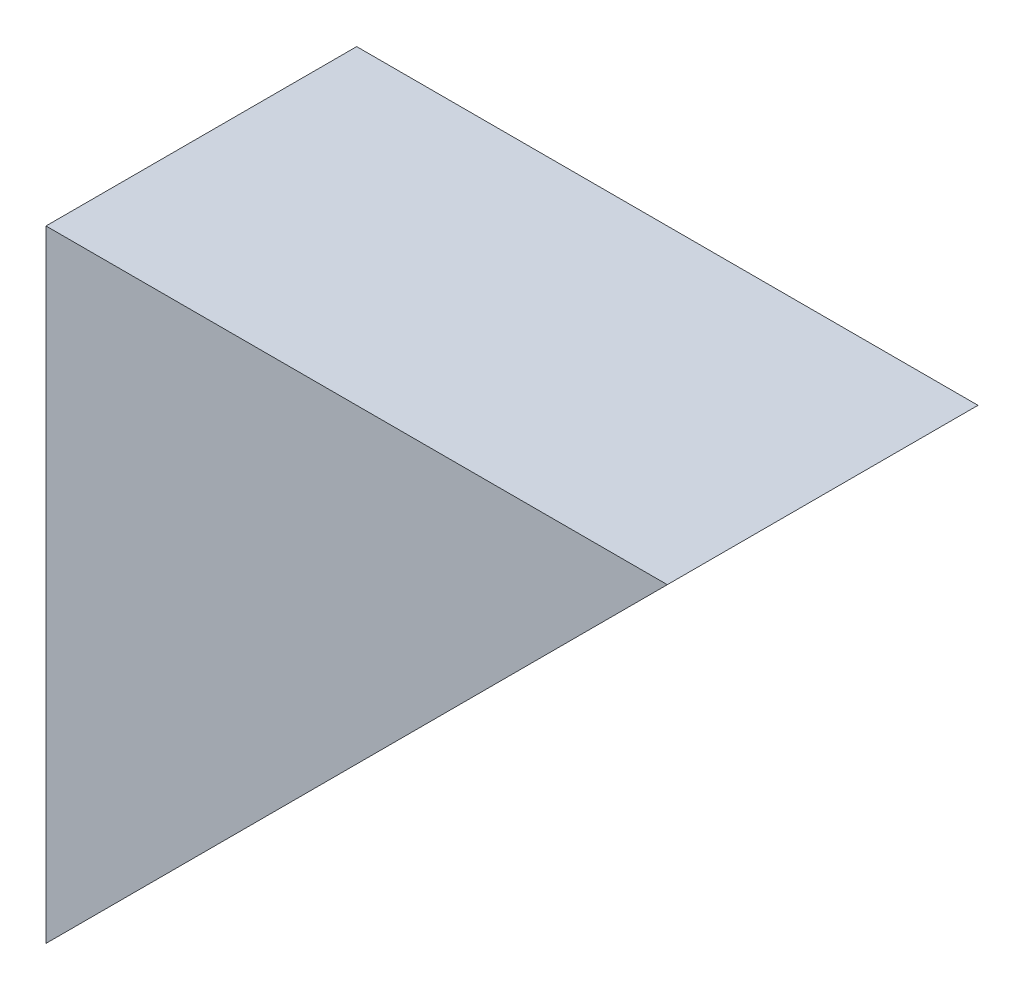
SolidWorks part; units mm, degrees
ref_plane "Front Plane" through (0, 0, 0) normal (0, 0, 1) x (1, 0, 0)
ref_plane "Top Plane" through (0, 0, 0) normal (0, 1, 0) x (1, 0, 0)
ref_plane "Right Plane" through (0, 0, 0) normal (1, 0, 0) x (0, 0, -1)
sketch "xs" plane through (0, 0, 0) normal (0, 0, 1) x (1, 0, 0)
  line L0 (-108.2045, 92.0764) -> (-108.2045, 66.6764)
  line L1 (-108.2045, 92.0764) -> (-82.8045, 92.0764)
  line L3 (-108.2045, 66.6764) -> (-82.8045, 92.0764)
extrude "Boss-Extrude2" add sketch "xs" against normal blind 12.7
sketch "Sketch5" plane through (-108.2045, 0, 0) normal (-1, 0, 0) x (0, 0, 1)
  circle A0 centre (-6.35, 79.3764) radius 2.25
  point P2 (0, 0)
  point P12 (-6.35, 79.3764)
  point P15 (-6.35, 79.3764)
  dimension "D1" = 0
extrude "Cut-Extrude1" cut sketch "Sketch5" against normal through all contours A0
ref_plane "Plane1" through (-99.3145, 0, 0) normal (-1, 0, 0) x (0, 0, 1)
sketch "Sketch6" plane through (-99.3145, 0, 0) normal (-1, 0, 0) x (0, 0, 1)
  circle A0 centre (-6.35, 79.3764) radius 4.5
extrude "Cut-Extrude2" cut sketch "Sketch6" against normal through all
